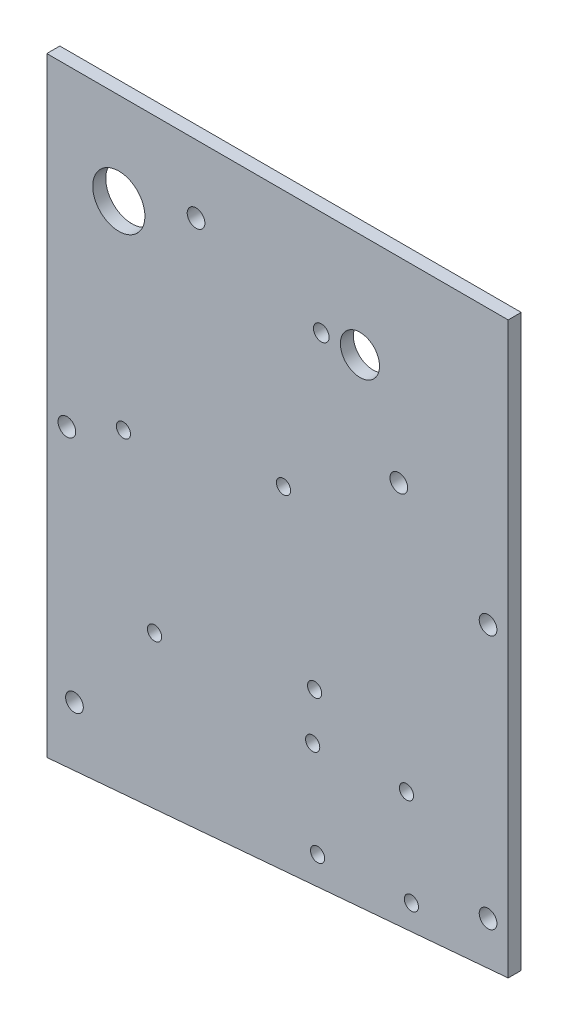
SolidWorks part; units mm, degrees
material "Acrylic (Medium-high impact)"
ref_plane "Front Plane" through (0, 0, 0) normal (0, 0, 1) x (1, 0, 0)
ref_plane "Top Plane" through (0, 0, 0) normal (0, 1, 0) x (1, 0, 0)
ref_plane "Right Plane" through (0, 0, 0) normal (1, 0, 0) x (0, 0, -1)
sketch "Sketch1" plane through (0, 0, 0) normal (0, 0, 1) x (1, 0, 0)
  line L4 (112.268, 0) -> (0, 0)
  line L5 (0, 0) -> (0, -148.336)
  line L6 (0, -148.336) -> (112.268, -138.684)
  line L7 (112.268, -138.684) -> (112.268, 0)
  line L8 (112.268, 0) -> (0, 0)
  line L9 (0, 0) -> (0, -148.336)
  line L10 (0, -148.336) -> (112.268, -138.684)
  line L11 (112.268, -138.684) -> (112.268, 0)
  dimension "D1" = 0
extrude "Boss-Extrude1" add sketch "Sketch1" against normal blind 3.175
hole_wizard "#6 Clearance Hole1" positions "Sketch3" profile "Sketch2" hole size "#6" standard "ANSI Inch" end condition through all
sketch "Sketch3" plane through (0, 0, 0) normal (0, 0, 1) x (1, 0, 0)
  point P0 (6.731, -133.35)
  point P3 (107.3785, -128.5875)
  point P6 (107.3785, -66.675)
  point P9 (4.8895, -76.2)
sketch "Sketch2" plane through (6.731, -133.35, 0) normal (1, 0, 0) x (0, -1, 0)
  line L0 (0, 0) -> (0, 3.175)
  line L1 (0, 3.175) -> (2.1526, 3.175)
  line L2 (2.1526, 3.175) -> (2.1526, 0)
  line L5 (2.1526, 0) -> (0, 0)
  line L11 (0, -6.35) -> (0, 107.95) construction
  dimension "Thru Hole Dia." = 4.3053
  dimension "Thru Hole Depth" = 3.175
hole_wizard "#4 Clearance Hole1" positions "Sketch5" profile "Sketch4" hole size "#4" standard "ANSI Inch" end condition through all
sketch "Sketch5" plane through (0, 0, 0) normal (0, 0, 1) x (1, 0, 0)
  point P0 (18.6445, -70.0322)
  point P3 (57.6028, -62.4595)
  point P6 (65.1755, -101.4178)
  point P9 (26.2172, -108.9905)
  point P12 (65.8919, -135.8375)
  point P15 (88.7205, -134.6411)
  point P18 (87.5241, -111.8125)
  point P21 (64.6955, -113.0089)
sketch "Sketch4" plane through (18.6445, -70.0322, 0) normal (1, 0, 0) x (0, -1, 0)
  line L0 (0, 0) -> (0, 3.175)
  line L1 (0, 3.175) -> (1.7272, 3.175)
  line L2 (1.7272, 3.175) -> (1.7272, 0)
  line L5 (1.7272, 0) -> (0, 0)
  line L11 (0, -6.35) -> (0, 107.95) construction
  dimension "Thru Hole Dia." = 3.4544
  dimension "Thru Hole Depth" = 3.175
hole_wizard "#6 Clearance Hole2" positions "Sketch7" profile "Sketch6" hole size "#6" standard "ANSI Inch" end condition through all
sketch "Sketch7" plane through (0, 0, 0) normal (0, 0, 1) x (1, 0, 0)
  point P0 (36.322, -16.51)
  point P3 (85.6615, -47.625)
sketch "Sketch6" plane through (36.322, -16.51, 0) normal (1, 0, 0) x (0, -1, 0)
  line L0 (0, 0) -> (0, 3.175)
  line L1 (0, 3.175) -> (2.1526, 3.175)
  line L2 (2.1526, 3.175) -> (2.1526, 0)
  line L5 (2.1526, 0) -> (0, 0)
  line L11 (0, -6.35) -> (0, 107.95) construction
  dimension "Thru Hole Dia." = 4.3053
  dimension "Thru Hole Depth" = 3.175
hole_wizard "3/8 (0.375) Diameter Hole1" positions "Sketch11" profile "Sketch10" hole size "3/8" standard "ANSI Inch" end condition through all
sketch "Sketch11" plane through (0, 0, 0) normal (0, 0, 1) x (1, 0, 0)
  point P0 (76.2, -25.4)
sketch "Sketch10" plane through (76.2, -25.4, 0) normal (1, 0, 0) x (0, -1, 0)
  line L0 (0, 0) -> (0, 3.175)
  line L1 (0, 3.175) -> (4.7625, 3.175)
  line L2 (4.7625, 3.175) -> (4.7625, 0)
  line L5 (4.7625, 0) -> (0, 0)
  line L11 (0, -6.35) -> (0, 107.95) construction
  dimension "Thru Hole Dia." = 9.525
  dimension "Thru Hole Depth" = 3.175
hole_wizard "1/2 (0.5) Diameter Hole1" positions "Sketch13" profile "Sketch12" hole size "1/2" standard "ANSI Inch" end condition through all
sketch "Sketch13" plane through (0, 0, 0) normal (0, 0, 1) x (1, 0, 0)
  point P0 (17.526, -22.352)
sketch "Sketch12" plane through (17.526, -22.352, 0) normal (1, 0, 0) x (0, -1, 0)
  line L0 (0, 0) -> (0, 3.175)
  line L1 (0, 3.175) -> (6.35, 3.175)
  line L2 (6.35, 3.175) -> (6.35, 0)
  line L5 (6.35, 0) -> (0, 0)
  line L11 (0, -6.35) -> (0, 107.95) construction
  dimension "Thru Hole Dia." = 12.7
  dimension "Thru Hole Depth" = 3.175
hole_wizard "OBOGS Rotary Anti Rotation Hole" positions "Sketch14" profile "Sketch15" legacy end condition through all
sketch "Sketch14" plane through (0, 0, -3.175) normal (0, 0, -1) x (-1, 0, 0)
  point P0 (-66.792, -25.4584)
  point P3 (-63.8909, -25.4859)
  point P4 (-66.349, -25.4859)
  point P5 (-66.792, -25.4584)
sketch "Sketch15" plane through (66.792, -25.4584, -3.175) normal (1, 0, 0) x (0, 1, 0)
  line L0 (0, 0) -> (0, 3.175)
  line L1 (0, 3.175) -> (1.905, 3.175)
  line L2 (1.905, 3.175) -> (1.905, 0)
  line L3 (1.905, 0) -> (0, 0)
  line L4 (0, 110) -> (0, -10) construction
  dimension "Diameter" = 3.81
  dimension "Depth" = 3.175
